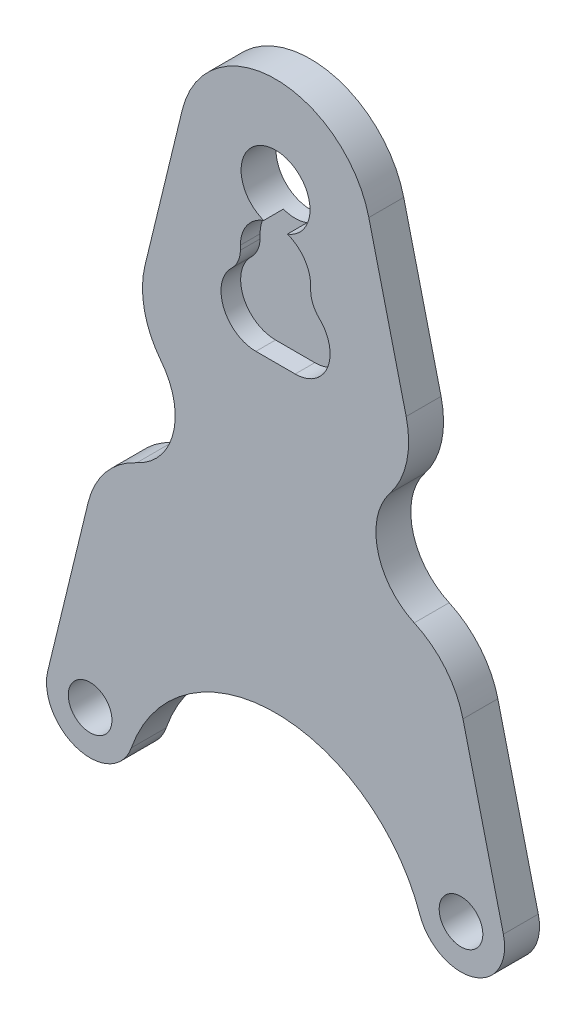
SolidWorks part; units mm, degrees
ref_plane "Спереди" through (0, 0, 0) normal (0, 0, 1) x (1, 0, 0)
ref_plane "Сверху" through (0, 0, 0) normal (0, 1, 0) x (1, 0, 0)
ref_plane "Справа" through (0, 0, 0) normal (1, 0, 0) x (0, 0, -1)
sketch "Эскиз1" plane through (0, 0, 0) normal (0, 0, 1) x (1, 0, 0)
  line L0 (0, 20) -> (0, -181.3933) construction
  line L6 (-21.3772, 5.1978) -> (-52.2169, -121.6374)
  line L8 (21.3772, 5.1978) -> (52.2169, -121.6374)
  circle A0 centre (0, 0) radius 7.9
  circle A1 centre (-42.5, -124) radius 5
  arc A2 (-21.3772, 5.1978) -> (21.3772, 5.1978) centre (0, 0) cw
  arc A3 (-52.2169, -121.6374) -> (-33.0556, -127.2867) centre (-42.5, -124) ccw
  circle A5 centre (42.5, -124) radius 5
  arc A6 (52.2169, -121.6374) -> (33.0556, -127.2867) centre (42.5, -124) cw
  arc A8 (-33.0556, -127.2867) -> (33.0556, -127.2867) centre (0, -138.7902) cw
  point P8 (0, -134)
  point P19 (0, -134)
  dimension "D1" = 15.8
  dimension "D4" = 22
  dimension "D6" = 10
  dimension "D5" = 10
  dimension "D7" = 35
  dimension "D2" = 85
  dimension "D3" = 124
extrude "Бобышка-Вытянуть1" add sketch "Эскиз1" along normal blind 8
sketch "Эскиз2" plane through (0, 0, 8) normal (0, 0, 1) x (1, 0, 0)
  line L0 (0, -16) -> (0, -54) construction
  line L3 (4.5, -34.3) -> (-4.5, -34.3)
  line L4 (0, 0) -> (0, -65.5898) construction
  line L5 (-8.05, -16) -> (-8.05, -15)
  line L6 (8.05, -16) -> (8.05, -15)
  arc A8 (8.05, -16) -> (10.0356, -20.5244) centre (14.4986, -15.8679) ccw
  arc A10 (10.0356, -20.5244) -> (4.5, -34.3) centre (4.5, -26.3) cw
  arc A12 (-10.0356, -20.5244) -> (-4.5, -34.3) centre (-4.5, -26.3) ccw
  arc A13 (-8.05, -16) -> (-10.0356, -20.5244) centre (-14.4986, -15.8679) cw
  arc A14 (-8.05, -15) -> (8.05, -15) centre (0, -15) cw
  point P8 (0, -35)
  point P20 (0, -34.3)
  dimension "D1" = 16
  dimension "D2" = 15.8679
  dimension "D4" = 16.1
  dimension "D6" = 15.8679
  dimension "D7" = 38
  dimension "D8" = 6.45
  dimension "D9" = 8
  dimension "D10" = 8
  dimension "D3" = 9
  dimension "D5" = 26.3
  dimension "D11" = 1
extrude "Вырез-Вытянуть1" cut sketch "Эскиз2" against normal blind 4.5
sketch "Эскиз3" plane through (0, 0, 8) normal (0, 0, 1) x (1, 0, 0)
  line L0 (0, 0) -> (0, -88.8714) construction
  circle A0 centre (-38, -56.3915) radius 15
  circle A1 centre (38, -56.3915) radius 15
  circle A2 centre (0, -26) radius 7.5 construction
  dimension "D1" = 68
  dimension "D2" = 30
  dimension "D4" = 15
  dimension "D3" = 38
  dimension "D5" = 26
extrude "Вырез-Вытянуть2" cut sketch "Эскиз3" against normal through all
fillet "Скругление1" radius 20 4 edges at (32.9207, -42.2776, 4) (39.9682, -71.2618, 4) (-39.9682, -71.2618, 4) (-32.9207, -42.2776, 4)
